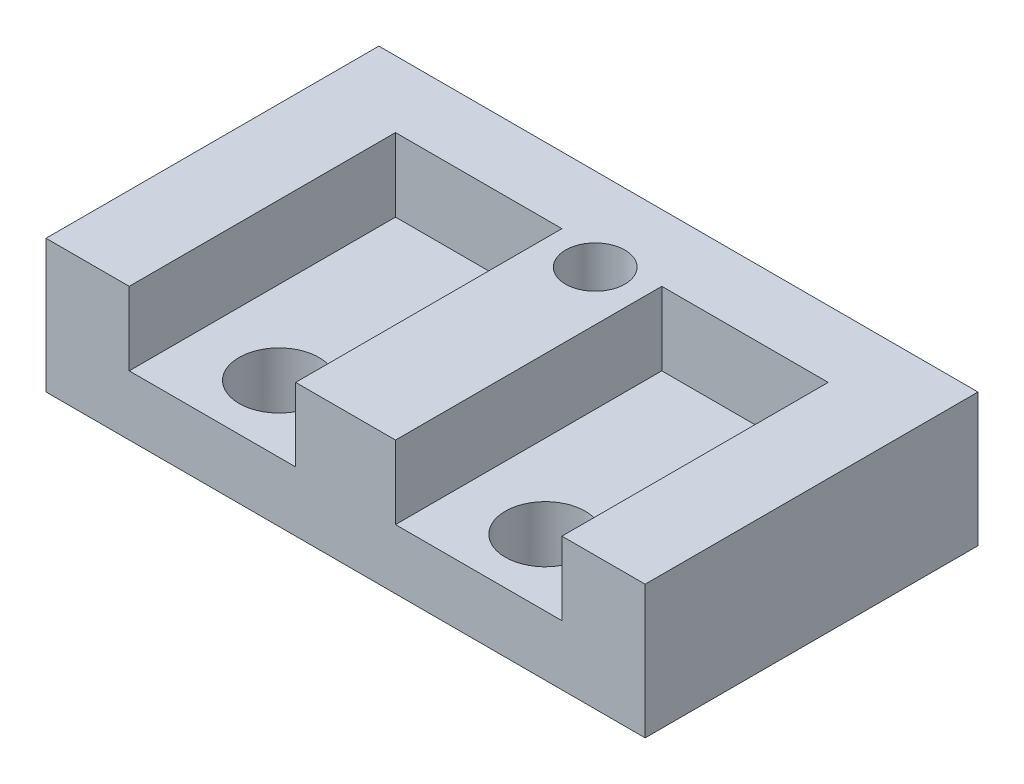
SolidWorks part; units mm, degrees
ref_plane "Front Plane" through (0, 0, 0) normal (0, 0, 1) x (1, 0, 0)
ref_plane "Top Plane" through (0, 0, 0) normal (0, 1, 0) x (1, 0, 0)
ref_plane "Right Plane" through (0, 0, 0) normal (1, 0, 0) x (0, 0, -1)
sketch "Sketch1" plane through (0, 0, 0) normal (0, 1, 0) x (1, 0, 0)
  line L1 (-11.43, -6.35) -> (11.43, -6.35)
  line L2 (-11.43, -6.35) -> (-11.43, 6.35)
  line L3 (-11.43, 6.35) -> (11.43, 6.35)
  line L4 (11.43, -6.35) -> (11.43, 6.35)
  line L5 (-11.43, -6.35) -> (11.43, 6.35) construction
  line L6 (-11.43, 6.35) -> (11.43, -6.35) construction
  point P0 (0, 0)
  dimension "D1" = 22.86
  dimension "D2" = 12.7
extrude "Boss-Extrude1" add sketch "Sketch1" along normal blind 5.08
hole_wizard "#4-40 Tapped Hole1" positions "Sketch3" profile "Sketch4" tap size "#4-40" standard "ANSI Inch"
sketch "Sketch3" plane through (0, 5.08, 0) normal (0, 1, 0) x (1, 0, 0)
  point P6 (0, 3.175)
  dimension "D1" = 3.175
sketch "Sketch4" plane through (0, 5.08, -3.175) normal (1, 0, 0) x (0, 0, 1)
  line L0 (0, 0) -> (0, 8.2738)
  line L1 (0, 8.2738) -> (1.1303, 7.5946)
  line L2 (1.1303, 7.5946) -> (1.1303, 0)
  line L5 (1.1303, 0) -> (0, 0)
  line L10 (0, 8.2738) -> (-1.1303, 7.5946) construction
  line L11 (0, -6.35) -> (0, 107.95) construction
  dimension "Tap Drill Dia." = 2.2606
  dimension "Tap Drill Depth" = 7.5946
  dimension "Drill Angle" = 118
cosmetic thread "Hole Thread1" parameters "D1"=5.6896, "D2"=2.8448
sketch "Sketch5" plane through (0, 5.08, 0) normal (0, 1, 0) x (1, 0, 0)
  line L0 (-11.43, -6.35) -> (11.43, -6.35) construction
  line L1 (-1.905, 3.81) -> (-8.255, 3.81)
  line L2 (-1.905, 3.81) -> (-1.905, -6.35)
  line L3 (-1.905, -6.35) -> (-8.255, -6.35)
  line L4 (-8.255, 3.81) -> (-8.255, -6.35)
  line L5 (0, 0) -> (0, 6.35) construction
  line L6 (11.43, 6.35) -> (-11.43, 6.35) construction
  line L7 (8.255, 3.81) -> (8.255, -6.35)
  line L8 (1.905, -6.35) -> (8.255, -6.35)
  line L9 (1.905, 3.81) -> (1.905, -6.35)
  line L10 (1.905, 3.81) -> (8.255, 3.81)
  dimension "D1" = 10.16
  dimension "D2" = 6.35
  dimension "D3" = 1.905
extrude "Cut-Extrude1" cut sketch "Sketch5" against normal blind 2.794
hole_wizard "#31 (0.12) Diameter Hole1" positions "Sketch6" profile "Sketch7" hole size "#31" standard "ANSI Inch"
sketch "Sketch6" plane through (0, 2.286, 0) normal (0, 1, 0) x (1, 0, 0)
  line L0 (0, 0) -> (0, -6.35) construction
  line L1 (-1.905, -6.35) -> (1.905, -6.35) construction
  line L3 (-8.255, -6.35) -> (-1.905, -6.35) construction
  point P0 (-5.08, -3.81)
  point P12 (-5.08, -6.35)
  point P14 (5.08, -3.81)
  dimension "D1" = 2.54
sketch "Sketch7" plane through (-5.08, 2.286, 3.81) normal (1, 0, 0) x (0, 0, 1)
  line L0 (0, 0) -> (0, 8.5103)
  line L1 (0, 8.5103) -> (1.524, 7.5946)
  line L2 (1.524, 7.5946) -> (1.524, 0)
  line L5 (1.524, 0) -> (0, 0)
  line L10 (0, 8.5103) -> (-1.524, 7.5946) construction
  line L11 (0, -6.35) -> (0, 107.95) construction
  dimension "Hole Dia." = 3.048
  dimension "Hole Depth" = 7.5946
  dimension "Drill Angle" = 118
